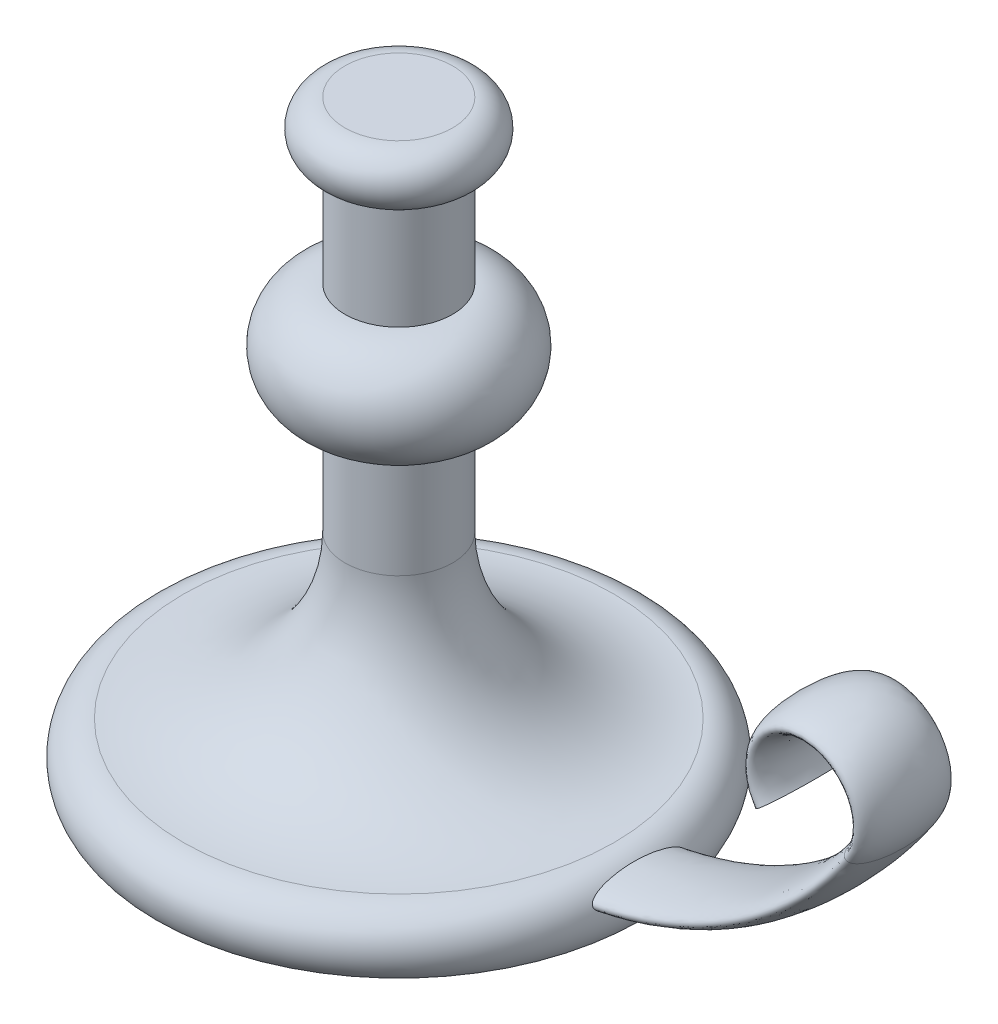
SolidWorks part; units mm, degrees
ref_plane "Front Plane" through (0, 0, 0) normal (0, 0, 1) x (1, 0, 0)
ref_plane "Top Plane" through (0, 0, 0) normal (0, 1, 0) x (1, 0, 0)
ref_plane "Right Plane" through (0, 0, 0) normal (1, 0, 0) x (0, 0, -1)
sketch "Sketch1" plane through (0, 0, 0) normal (0, 0, 1) x (1, 0, 0)
  line L0 (0, 220) -> (0, 0)
  line L1 (0, 220) -> (20, 220)
  line L2 (0, 0) -> (90, 0)
  line L3 (20, 200) -> (20, 160)
  line L4 (20, 120) -> (20, 80)
  arc A0 (20, 220) -> (20, 200) centre (20, 210) cw
  arc A1 (20, 160) -> (20, 120) centre (20, 140) cw
  arc A2 (20, 80) -> (80, 20) centre (80, 80) ccw
  arc A3 (80, 20) -> (90, 0) centre (80, 7.5) cw
  point P11 (91.1803, 13.0902)
  dimension "D7" = 80
  dimension "D9" = 60
  dimension "D1" = 220
  dimension "D2" = 90
  dimension "D3" = 20
  dimension "D4" = 10
  dimension "D5" = 20
  dimension "D6" = 40
  dimension "D8" = 12.5
revolve "Revolve1" add sketch "Sketch1" angle 360 about L0
sketch "Sketch2" plane through (0, 0, 0) normal (0, 0, 1) x (1, 0, 0)
  line L0 (0, 10) -> (60, 10)
  line L1 (-90, 0) -> (90, 0) construction
  arc A0 (60, 10) -> (183.5921, 75) centre (60, 160) ccw
  arc A1 (183.5921, 75) -> (150.6342, 75) centre (167.1131, 86.3333) ccw
  point P6 (0, 13.8878)
  point P9 (0, 0)
  dimension "D2" = 150
  dimension "D4" = 20
  dimension "D1" = 60
  dimension "D3" = 65
  dimension "D5" = 10
sketch "Sketch4" plane through (0, 0, 0) normal (1, 0, 0) x (0, 0, -1)
  line L0 (0, 75) -> (0, 10) construction
  ellipse E0 centre (0, 10) end of major axis (17.5, 10) minor radius 5
  point P1 (0, 0)
  dimension "D1" = 35
  dimension "D2" = 10
sweep "Sweep1" add profiles "Sketch4" path "Sketch2"
